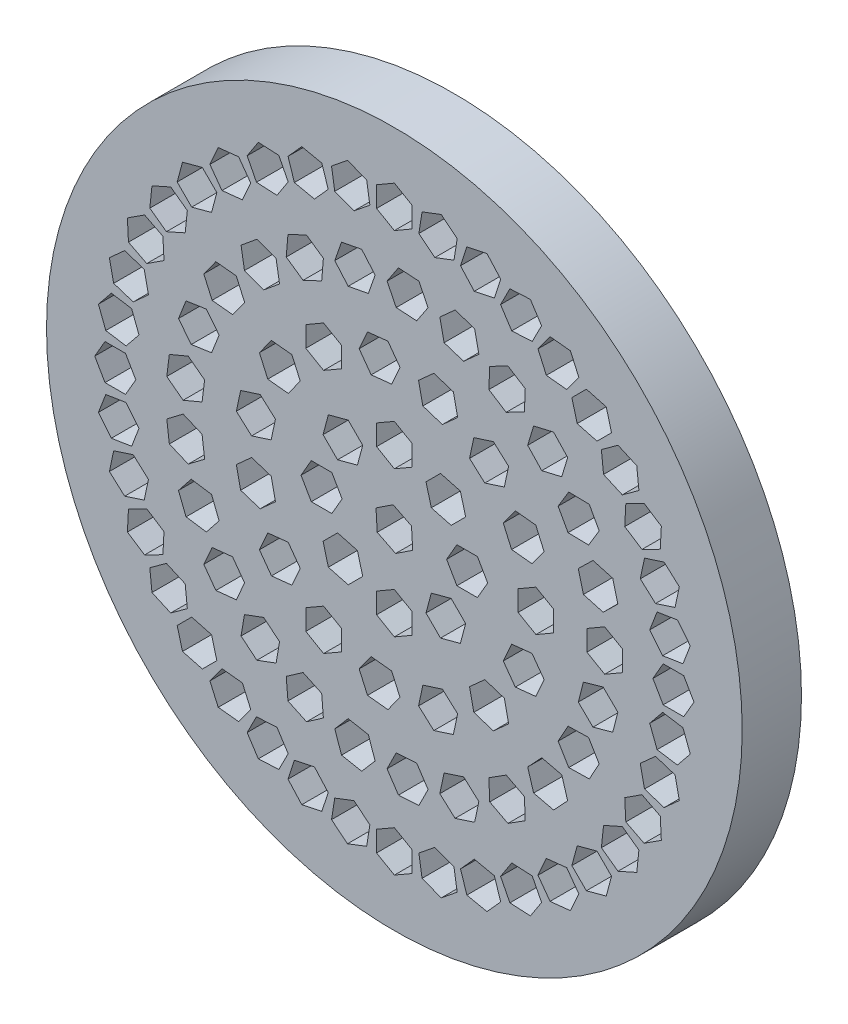
SolidWorks part; units mm, degrees
material "Balsa"
ref_plane "Front Plane" through (0, 0, 0) normal (0, 0, 1) x (1, 0, 0)
ref_plane "Top Plane" through (0, 0, 0) normal (0, 1, 0) x (1, 0, 0)
ref_plane "Right Plane" through (0, 0, 0) normal (1, 0, 0) x (0, 0, -1)
sketch "Sketch1" plane through (0, 0, 0) normal (0, 0, 1) x (1, 0, 0)
  line L0 (0, 44.3149) -> (0, -33.0251) construction
  line L1 (-45.3381, 0) -> (52.4482, 0) construction
  line L2 (29.34, 0) -> (23.54, 0) construction
  line L3 (23.54, 0) -> (17.74, 0) construction
  line L4 (17.74, 0) -> (11.94, 0) construction
  line L5 (11.94, 0) -> (6.14, 0) construction
  line L6 (3.1169, -3.1169) -> (2.6686, -4.7899)
  line L7 (7.8721, 0) -> (7.006, 1.5)
  line L8 (7.006, 1.5) -> (5.274, 1.5)
  line L9 (5.274, 1.5) -> (4.4079, 0)
  line L10 (4.4079, 0) -> (5.274, -1.5)
  line L11 (5.274, -1.5) -> (7.006, -1.5)
  line L12 (7.006, -1.5) -> (7.8721, 0)
  line L13 (11.94, -1.7321) -> (13.44, -0.866)
  line L14 (13.44, -0.866) -> (13.44, 0.866)
  line L15 (13.44, 0.866) -> (11.94, 1.7321)
  line L16 (11.94, 1.7321) -> (10.44, 0.866)
  line L17 (10.44, 0.866) -> (10.44, -0.866)
  line L18 (10.44, -0.866) -> (11.94, -1.7321)
  line L19 (17.74, -1.7321) -> (19.24, -0.866)
  line L20 (19.24, -0.866) -> (19.24, 0.866)
  line L21 (19.24, 0.866) -> (17.74, 1.7321)
  line L22 (17.74, 1.7321) -> (16.24, 0.866)
  line L23 (16.24, 0.866) -> (16.24, -0.866)
  line L24 (16.24, -0.866) -> (17.74, -1.7321)
  line L25 (21.8079, 0) -> (22.674, -1.5)
  line L26 (22.674, -1.5) -> (24.406, -1.5)
  line L27 (24.406, -1.5) -> (25.2721, 0)
  line L28 (25.2721, 0) -> (24.406, 1.5)
  line L29 (24.406, 1.5) -> (22.674, 1.5)
  line L30 (22.674, 1.5) -> (21.8079, 0)
  line L31 (4.7899, -2.6686) -> (3.1169, -3.1169)
  line L32 (6.0147, -3.8933) -> (4.7899, -2.6686)
  line L33 (5.5664, -5.5664) -> (6.0147, -3.8933)
  line L34 (3.8933, -6.0147) -> (5.5664, -5.5664)
  line L35 (2.6686, -4.7899) -> (3.8933, -6.0147)
  line L36 (0, -4.4079) -> (-1.5, -5.274)
  line L37 (1.5, -5.274) -> (0, -4.4079)
  line L38 (1.5, -7.006) -> (1.5, -5.274)
  line L39 (0, -7.8721) -> (1.5, -7.006)
  line L40 (-1.5, -7.006) -> (0, -7.8721)
  line L41 (-1.5, -5.274) -> (-1.5, -7.006)
  line L42 (-3.1169, -3.1169) -> (-4.7899, -2.6686)
  line L43 (-2.6686, -4.7899) -> (-3.1169, -3.1169)
  line L44 (-3.8933, -6.0147) -> (-2.6686, -4.7899)
  line L45 (-5.5664, -5.5664) -> (-3.8933, -6.0147)
  line L46 (-6.0147, -3.8933) -> (-5.5664, -5.5664)
  line L47 (-4.7899, -2.6686) -> (-6.0147, -3.8933)
  line L48 (-4.4079, 0) -> (-5.274, 1.5)
  line L49 (-5.274, -1.5) -> (-4.4079, 0)
  line L50 (-7.006, -1.5) -> (-5.274, -1.5)
  line L51 (-7.8721, 0) -> (-7.006, -1.5)
  line L52 (-7.006, 1.5) -> (-7.8721, 0)
  line L53 (-5.274, 1.5) -> (-7.006, 1.5)
  line L54 (-3.1169, 3.1169) -> (-2.6686, 4.7899)
  line L55 (-4.7899, 2.6686) -> (-3.1169, 3.1169)
  line L56 (-6.0147, 3.8933) -> (-4.7899, 2.6686)
  line L57 (-5.5664, 5.5664) -> (-6.0147, 3.8933)
  line L58 (-3.8933, 6.0147) -> (-5.5664, 5.5664)
  line L59 (-2.6686, 4.7899) -> (-3.8933, 6.0147)
  line L60 (0, 4.4079) -> (1.5, 5.274)
  line L61 (-1.5, 5.274) -> (0, 4.4079)
  line L62 (-1.5, 7.006) -> (-1.5, 5.274)
  line L63 (0, 7.8721) -> (-1.5, 7.006)
  line L64 (1.5, 7.006) -> (0, 7.8721)
  line L65 (1.5, 5.274) -> (1.5, 7.006)
  line L66 (3.1169, 3.1169) -> (4.7899, 2.6686)
  line L67 (2.6686, 4.7899) -> (3.1169, 3.1169)
  line L68 (3.8933, 6.0147) -> (2.6686, 4.7899)
  line L69 (5.5664, 5.5664) -> (3.8933, 6.0147)
  line L70 (6.0147, 3.8933) -> (5.5664, 5.5664)
  line L71 (4.7899, 2.6686) -> (6.0147, 3.8933)
  line L72 (9.1852, -5.0375) -> (10.2032, -6.4387)
  line L73 (1.5492, -0.7746) -> (1.4454, 0.9543)
  line L74 (1.4454, 0.9543) -> (-0.1038, 1.7289)
  line L75 (-0.1038, 1.7289) -> (-1.5492, 0.7746)
  line L76 (-1.5492, 0.7746) -> (-1.4454, -0.9543)
  line L77 (-1.4454, -0.9543) -> (0.1038, -1.7289)
  line L78 (0.1038, -1.7289) -> (1.5492, -0.7746)
  line L79 (10.2032, -6.4387) -> (11.9258, -6.2577)
  line L80 (11.9258, -6.2577) -> (12.6303, -4.6754)
  line L81 (12.6303, -4.6754) -> (11.6122, -3.2741)
  line L82 (11.6122, -3.2741) -> (9.8897, -3.4552)
  line L83 (9.8897, -3.4552) -> (9.1852, -5.0375)
  line L84 (6.3421, -8.3379) -> (6.7023, -10.0321)
  line L85 (6.7023, -10.0321) -> (8.3495, -10.5674)
  line L86 (8.3495, -10.5674) -> (9.6367, -9.4084)
  line L87 (9.6367, -9.4084) -> (9.2766, -7.7142)
  line L88 (9.2766, -7.7142) -> (7.6293, -7.1789)
  line L89 (7.6293, -7.1789) -> (6.3421, -8.3379)
  line L90 (2.4025, -10.1966) -> (2.0424, -11.8908)
  line L91 (2.0424, -11.8908) -> (3.3295, -13.0498)
  line L92 (3.3295, -13.0498) -> (4.9768, -12.5146)
  line L93 (4.9768, -12.5146) -> (5.3369, -10.8204)
  line L94 (5.3369, -10.8204) -> (4.0498, -9.6614)
  line L95 (4.0498, -9.6614) -> (2.4025, -10.1966)
  line L96 (-1.9526, -10.2923) -> (-2.9706, -11.6935)
  line L97 (-2.9706, -11.6935) -> (-2.2661, -13.2758)
  line L98 (-2.2661, -13.2758) -> (-0.5436, -13.4569)
  line L99 (-0.5436, -13.4569) -> (0.4745, -12.0556)
  line L100 (0.4745, -12.0556) -> (-0.23, -10.4733)
  line L101 (-0.23, -10.4733) -> (-1.9526, -10.2923)
  line L102 (-5.97, -8.6083) -> (-7.47, -9.4743)
  line L103 (-7.47, -9.4743) -> (-7.47, -11.2064)
  line L104 (-7.47, -11.2064) -> (-5.97, -12.0724)
  line L105 (-5.97, -12.0724) -> (-4.47, -11.2064)
  line L106 (-4.47, -11.2064) -> (-4.47, -9.4743)
  line L107 (-4.47, -9.4743) -> (-5.97, -8.6083)
  line L108 (-8.9552, -5.4358) -> (-10.6777, -5.6169)
  line L109 (-10.6777, -5.6169) -> (-11.3822, -7.1992)
  line L110 (-11.3822, -7.1992) -> (-10.3642, -8.6005)
  line L111 (-10.3642, -8.6005) -> (-8.6416, -8.4194)
  line L112 (-8.6416, -8.4194) -> (-7.9371, -6.8371)
  line L113 (-7.9371, -6.8371) -> (-8.9552, -5.4358)
  line L114 (-10.3919, -1.3235) -> (-12.0392, -0.7883)
  line L115 (-12.0392, -0.7883) -> (-13.3264, -1.9472)
  line L116 (-13.3264, -1.9472) -> (-12.9662, -3.6414)
  line L117 (-12.9662, -3.6414) -> (-11.319, -4.1767)
  line L118 (-11.319, -4.1767) -> (-10.0318, -3.0177)
  line L119 (-10.0318, -3.0177) -> (-10.3919, -1.3235)
  line L120 (-10.0318, 3.0177) -> (-11.319, 4.1767)
  line L121 (-11.319, 4.1767) -> (-12.9662, 3.6414)
  line L122 (-12.9662, 3.6414) -> (-13.3264, 1.9472)
  line L123 (-13.3264, 1.9472) -> (-12.0392, 0.7883)
  line L124 (-12.0392, 0.7883) -> (-10.3919, 1.3235)
  line L125 (-10.3919, 1.3235) -> (-10.0318, 3.0177)
  line L126 (-7.9371, 6.8371) -> (-8.6416, 8.4194)
  line L127 (-8.6416, 8.4194) -> (-10.3642, 8.6005)
  line L128 (-10.3642, 8.6005) -> (-11.3822, 7.1992)
  line L129 (-11.3822, 7.1992) -> (-10.6777, 5.6169)
  line L130 (-10.6777, 5.6169) -> (-8.9552, 5.4358)
  line L131 (-8.9552, 5.4358) -> (-7.9371, 6.8371)
  line L132 (-4.47, 9.4743) -> (-4.47, 11.2064)
  line L133 (-4.47, 11.2064) -> (-5.97, 12.0724)
  line L134 (-5.97, 12.0724) -> (-7.47, 11.2064)
  line L135 (-7.47, 11.2064) -> (-7.47, 9.4743)
  line L136 (-7.47, 9.4743) -> (-5.97, 8.6083)
  line L137 (-5.97, 8.6083) -> (-4.47, 9.4743)
  line L138 (-0.23, 10.4733) -> (0.4745, 12.0556)
  line L139 (0.4745, 12.0556) -> (-0.5436, 13.4569)
  line L140 (-0.5436, 13.4569) -> (-2.2661, 13.2758)
  line L141 (-2.2661, 13.2758) -> (-2.9706, 11.6935)
  line L142 (-2.9706, 11.6935) -> (-1.9526, 10.2923)
  line L143 (-1.9526, 10.2923) -> (-0.23, 10.4733)
  line L144 (4.0498, 9.6614) -> (5.3369, 10.8204)
  line L145 (5.3369, 10.8204) -> (4.9768, 12.5146)
  line L146 (4.9768, 12.5146) -> (3.3295, 13.0498)
  line L147 (3.3295, 13.0498) -> (2.0424, 11.8908)
  line L148 (2.0424, 11.8908) -> (2.4025, 10.1966)
  line L149 (2.4025, 10.1966) -> (4.0498, 9.6614)
  line L150 (7.6293, 7.1789) -> (9.2766, 7.7142)
  line L151 (9.2766, 7.7142) -> (9.6367, 9.4084)
  line L152 (9.6367, 9.4084) -> (8.3495, 10.5674)
  line L153 (8.3495, 10.5674) -> (6.7023, 10.0321)
  line L154 (6.7023, 10.0321) -> (6.3421, 8.3379)
  line L155 (6.3421, 8.3379) -> (7.6293, 7.1789)
  line L156 (9.8897, 3.4552) -> (11.6122, 3.2741)
  line L157 (11.6122, 3.2741) -> (12.6303, 4.6754)
  line L158 (12.6303, 4.6754) -> (11.9258, 6.2577)
  line L159 (11.9258, 6.2577) -> (10.2032, 6.4387)
  line L160 (10.2032, 6.4387) -> (9.1852, 5.0375)
  line L161 (9.1852, 5.0375) -> (9.8897, 3.4552)
  line L162 (16.7519, -6.0894) -> (18.4202, -5.6236)
  line L163 (15.5144, -4.8775) -> (16.7519, -6.0894)
  line L164 (15.9452, -3.1999) -> (15.5144, -4.8775)
  line L165 (17.6134, -2.7341) -> (15.9452, -3.1999)
  line L166 (18.8509, -3.946) -> (17.6134, -2.7341)
  line L167 (18.4202, -5.6236) -> (18.8509, -3.946)
  line L168 (14.7113, -10.0641) -> (16.4429, -10.0278)
  line L169 (13.814, -8.5826) -> (14.7113, -10.0641)
  line L170 (14.6484, -7.0648) -> (13.814, -8.5826)
  line L171 (16.3801, -7.0285) -> (14.6484, -7.0648)
  line L172 (17.2774, -8.51) -> (16.3801, -7.0285)
  line L173 (16.4429, -10.0278) -> (17.2774, -8.51)
  line L174 (11.7462, -13.4065) -> (13.4325, -13.802)
  line L175 (11.2456, -11.7484) -> (11.7462, -13.4065)
  line L176 (12.4313, -10.4857) -> (11.2456, -11.7484)
  line L177 (14.1176, -10.8813) -> (12.4313, -10.4857)
  line L178 (14.6182, -12.5394) -> (14.1176, -10.8813)
  line L179 (13.4325, -13.802) -> (14.6182, -12.5394)
  line L180 (8.0431, -15.9065) -> (9.5781, -16.7089)
  line L181 (7.9706, -14.1759) -> (8.0431, -15.9065)
  line L182 (9.433, -13.2478) -> (7.9706, -14.1759)
  line L183 (10.968, -14.0503) -> (9.433, -13.2478)
  line L184 (11.0405, -15.7808) -> (10.968, -14.0503)
  line L185 (9.5781, -16.7089) -> (11.0405, -15.7808)
  line L186 (3.8347, -17.407) -> (5.1218, -18.5659)
  line L187 (4.1948, -15.7128) -> (3.8347, -17.407)
  line L188 (5.8421, -15.1775) -> (4.1948, -15.7128)
  line L189 (7.1292, -16.3365) -> (5.8421, -15.1775)
  line L190 (6.7691, -18.0307) -> (7.1292, -16.3365)
  line L191 (5.1218, -18.5659) -> (6.7691, -18.0307)
  line L192 (-0.6147, -17.8138) -> (0.3438, -19.2564)
  line L193 (0.1554, -16.2623) -> (-0.6147, -17.8138)
  line L194 (1.884, -16.1536) -> (0.1554, -16.2623)
  line L195 (2.8425, -17.5962) -> (1.884, -16.1536)
  line L196 (2.0724, -19.1477) -> (2.8425, -17.5962)
  line L197 (0.3438, -19.2564) -> (2.0724, -19.1477)
  line L198 (-5.0255, -17.1012) -> (-4.4559, -18.7369)
  line L199 (-3.8938, -15.7901) -> (-5.0255, -17.1012)
  line L200 (-2.1924, -16.1146) -> (-3.8938, -15.7901)
  line L201 (-1.6228, -17.7503) -> (-2.1924, -16.1146)
  line L202 (-2.7545, -19.0615) -> (-1.6228, -17.7503)
  line L203 (-4.4559, -18.7369) -> (-2.7545, -19.0615)
  line L204 (-9.1205, -15.3142) -> (-8.9756, -17.0401)
  line L205 (-7.6983, -14.3257) -> (-9.1205, -15.3142)
  line L206 (-6.1311, -15.0631) -> (-7.6983, -14.3257)
  line L207 (-5.9861, -16.7891) -> (-6.1311, -15.0631)
  line L208 (-7.4084, -17.7776) -> (-5.9861, -16.7891)
  line L209 (-8.9756, -17.0401) -> (-7.4084, -17.7776)
  line L210 (-12.6425, -12.5649) -> (-12.9313, -14.2726)
  line L211 (-11.019, -11.9611) -> (-12.6425, -12.5649)
  line L212 (-9.6845, -13.0652) -> (-11.019, -11.9611)
  line L213 (-9.9733, -14.773) -> (-9.6845, -13.0652)
  line L214 (-11.5968, -15.3767) -> (-9.9733, -14.773)
  line L215 (-12.9313, -14.2726) -> (-11.5968, -15.3767)
  line L216 (-15.37, -9.0261) -> (-16.0745, -10.6084)
  line L217 (-13.6475, -8.845) -> (-15.37, -9.0261)
  line L218 (-12.6294, -10.2463) -> (-13.6475, -8.845)
  line L219 (-13.3339, -11.8286) -> (-12.6294, -10.2463)
  line L220 (-15.0565, -12.0096) -> (-13.3339, -11.8286)
  line L221 (-16.0745, -10.6084) -> (-15.0565, -12.0096)
  line L222 (-17.1318, -4.9201) -> (-18.2077, -6.2775)
  line L223 (-15.4184, -5.1731) -> (-17.1318, -4.9201)
  line L224 (-14.7808, -6.7836) -> (-15.4184, -5.1731)
  line L225 (-15.8566, -8.1409) -> (-14.7808, -6.7836)
  line L226 (-17.5701, -7.8879) -> (-15.8566, -8.1409)
  line L227 (-18.2077, -6.2775) -> (-17.5701, -7.8879)
  line L228 (-17.8172, -0.505) -> (-19.1968, -1.5522)
  line L229 (-16.2205, -1.1762) -> (-17.8172, -0.505)
  line L230 (-16.0034, -2.8946) -> (-16.2205, -1.1762)
  line L231 (-17.383, -3.9418) -> (-16.0034, -2.8946)
  line L232 (-18.9797, -3.2706) -> (-17.383, -3.9418)
  line L233 (-19.1968, -1.5522) -> (-18.9797, -3.2706)
  line L234 (-17.383, 3.9418) -> (-18.9797, 3.2706)
  line L235 (-16.0034, 2.8946) -> (-17.383, 3.9418)
  line L236 (-16.2205, 1.1762) -> (-16.0034, 2.8946)
  line L237 (-17.8172, 0.505) -> (-16.2205, 1.1762)
  line L238 (-19.1968, 1.5522) -> (-17.8172, 0.505)
  line L239 (-18.9797, 3.2706) -> (-19.1968, 1.5522)
  line L240 (-15.8566, 8.1409) -> (-17.5701, 7.8879)
  line L241 (-14.7808, 6.7836) -> (-15.8566, 8.1409)
  line L242 (-15.4184, 5.1731) -> (-14.7808, 6.7836)
  line L243 (-17.1318, 4.9201) -> (-15.4184, 5.1731)
  line L244 (-18.2077, 6.2775) -> (-17.1318, 4.9201)
  line L245 (-17.5701, 7.8879) -> (-18.2077, 6.2775)
  line L246 (-13.3339, 11.8286) -> (-15.0565, 12.0096)
  line L247 (-12.6294, 10.2463) -> (-13.3339, 11.8286)
  line L248 (-13.6475, 8.845) -> (-12.6294, 10.2463)
  line L249 (-15.37, 9.0261) -> (-13.6475, 8.845)
  line L250 (-16.0745, 10.6084) -> (-15.37, 9.0261)
  line L251 (-15.0565, 12.0096) -> (-16.0745, 10.6084)
  line L252 (-9.9733, 14.773) -> (-11.5968, 15.3767)
  line L253 (-9.6845, 13.0652) -> (-9.9733, 14.773)
  line L254 (-11.019, 11.9611) -> (-9.6845, 13.0652)
  line L255 (-12.6425, 12.5649) -> (-11.019, 11.9611)
  line L256 (-12.9313, 14.2726) -> (-12.6425, 12.5649)
  line L257 (-11.5968, 15.3767) -> (-12.9313, 14.2726)
  line L258 (-5.9861, 16.7891) -> (-7.4084, 17.7776)
  line L259 (-6.1311, 15.0631) -> (-5.9861, 16.7891)
  line L260 (-7.6983, 14.3257) -> (-6.1311, 15.0631)
  line L261 (-9.1205, 15.3142) -> (-7.6983, 14.3257)
  line L262 (-8.9756, 17.0401) -> (-9.1205, 15.3142)
  line L263 (-7.4084, 17.7776) -> (-8.9756, 17.0401)
  line L264 (-1.6228, 17.7503) -> (-2.7545, 19.0615)
  line L265 (-2.1924, 16.1146) -> (-1.6228, 17.7503)
  line L266 (-3.8938, 15.7901) -> (-2.1924, 16.1146)
  line L267 (-5.0255, 17.1012) -> (-3.8938, 15.7901)
  line L268 (-4.4559, 18.7369) -> (-5.0255, 17.1012)
  line L269 (-2.7545, 19.0615) -> (-4.4559, 18.7369)
  line L270 (2.8425, 17.5962) -> (2.0724, 19.1477)
  line L271 (1.884, 16.1536) -> (2.8425, 17.5962)
  line L272 (0.1554, 16.2623) -> (1.884, 16.1536)
  line L273 (-0.6147, 17.8138) -> (0.1554, 16.2623)
  line L274 (0.3438, 19.2564) -> (-0.6147, 17.8138)
  line L275 (2.0724, 19.1477) -> (0.3438, 19.2564)
  line L276 (7.1292, 16.3365) -> (6.7691, 18.0307)
  line L277 (5.8421, 15.1775) -> (7.1292, 16.3365)
  line L278 (4.1948, 15.7128) -> (5.8421, 15.1775)
  line L279 (3.8347, 17.407) -> (4.1948, 15.7128)
  line L280 (5.1218, 18.5659) -> (3.8347, 17.407)
  line L281 (6.7691, 18.0307) -> (5.1218, 18.5659)
  line L282 (10.968, 14.0503) -> (11.0405, 15.7808)
  line L283 (9.433, 13.2478) -> (10.968, 14.0503)
  line L284 (7.9706, 14.1759) -> (9.433, 13.2478)
  line L285 (8.0431, 15.9065) -> (7.9706, 14.1759)
  line L286 (9.5781, 16.7089) -> (8.0431, 15.9065)
  line L287 (11.0405, 15.7808) -> (9.5781, 16.7089)
  line L288 (14.1176, 10.8813) -> (14.6182, 12.5394)
  line L289 (12.4313, 10.4857) -> (14.1176, 10.8813)
  line L290 (11.2456, 11.7484) -> (12.4313, 10.4857)
  line L291 (11.7462, 13.4065) -> (11.2456, 11.7484)
  line L292 (13.4325, 13.802) -> (11.7462, 13.4065)
  line L293 (14.6182, 12.5394) -> (13.4325, 13.802)
  line L294 (16.3801, 7.0285) -> (17.2774, 8.51)
  line L295 (14.6484, 7.0648) -> (16.3801, 7.0285)
  line L296 (13.814, 8.5826) -> (14.6484, 7.0648)
  line L297 (14.7113, 10.0641) -> (13.814, 8.5826)
  line L298 (16.4429, 10.0278) -> (14.7113, 10.0641)
  line L299 (17.2774, 8.51) -> (16.4429, 10.0278)
  line L300 (17.6134, 2.7341) -> (18.8509, 3.946)
  line L301 (15.9452, 3.1999) -> (17.6134, 2.7341)
  line L302 (15.5144, 4.8775) -> (15.9452, 3.1999)
  line L303 (16.7519, 6.0894) -> (15.5144, 4.8775)
  line L304 (18.4202, 5.6236) -> (16.7519, 6.0894)
  line L305 (18.8509, 3.946) -> (18.4202, 5.6236)
  line L306 (21.5395, -3.4115) -> (22.1602, -5.0285)
  line L307 (22.6295, -2.0655) -> (21.5395, -3.4115)
  line L308 (24.3402, -2.3364) -> (22.6295, -2.0655)
  line L309 (24.9609, -3.9534) -> (24.3402, -2.3364)
  line L310 (23.8709, -5.2995) -> (24.9609, -3.9534)
  line L311 (22.1602, -5.0285) -> (23.8709, -5.2995)
  line L312 (20.7406, -6.739) -> (21.1007, -8.4332)
  line L313 (22.0278, -5.5801) -> (20.7406, -6.739)
  line L314 (23.675, -6.1153) -> (22.0278, -5.5801)
  line L315 (24.0351, -7.8095) -> (23.675, -6.1153)
  line L316 (22.748, -8.9685) -> (24.0351, -7.8095)
  line L317 (21.1007, -8.4332) -> (22.748, -8.9685)
  line L318 (19.431, -9.9006) -> (19.5217, -11.6303)
  line L319 (20.8836, -8.9573) -> (19.431, -9.9006)
  line L320 (22.4269, -9.7436) -> (20.8836, -8.9573)
  line L321 (22.5176, -11.4733) -> (22.4269, -9.7436)
  line L322 (21.0649, -12.4166) -> (22.5176, -11.4733)
  line L323 (19.5217, -11.6303) -> (21.0649, -12.4166)
  line L324 (17.643, -12.8184) -> (17.462, -14.541)
  line L325 (19.2253, -12.1139) -> (17.643, -12.8184)
  line L326 (20.6266, -13.132) -> (19.2253, -12.1139)
  line L327 (20.4455, -14.8545) -> (20.6266, -13.132)
  line L328 (18.8632, -15.559) -> (20.4455, -14.8545)
  line L329 (17.462, -14.541) -> (18.8632, -15.559)
  line L330 (15.4205, -15.4205) -> (14.9723, -17.0936)
  line L331 (17.0936, -14.9723) -> (15.4205, -15.4205)
  line L332 (18.3183, -16.197) -> (17.0936, -14.9723)
  line L333 (17.87, -17.87) -> (18.3183, -16.197)
  line L334 (16.197, -18.3183) -> (17.87, -17.87)
  line L335 (14.9723, -17.0936) -> (16.197, -18.3183)
  line L336 (12.8184, -17.643) -> (12.1139, -19.2253)
  line L337 (14.541, -17.462) -> (12.8184, -17.643)
  line L338 (15.559, -18.8632) -> (14.541, -17.462)
  line L339 (14.8545, -20.4455) -> (15.559, -18.8632)
  line L340 (13.132, -20.6266) -> (14.8545, -20.4455)
  line L341 (12.1139, -19.2253) -> (13.132, -20.6266)
  line L342 (9.9006, -19.431) -> (8.9573, -20.8836)
  line L343 (11.6303, -19.5217) -> (9.9006, -19.431)
  line L344 (12.4166, -21.0649) -> (11.6303, -19.5217)
  line L345 (11.4733, -22.5176) -> (12.4166, -21.0649)
  line L346 (9.7436, -22.4269) -> (11.4733, -22.5176)
  line L347 (8.9573, -20.8836) -> (9.7436, -22.4269)
  line L348 (6.739, -20.7406) -> (5.5801, -22.0278)
  line L349 (8.4332, -21.1007) -> (6.739, -20.7406)
  line L350 (8.9685, -22.748) -> (8.4332, -21.1007)
  line L351 (7.8095, -24.0351) -> (8.9685, -22.748)
  line L352 (6.1153, -23.675) -> (7.8095, -24.0351)
  line L353 (5.5801, -22.0278) -> (6.1153, -23.675)
  line L354 (3.4115, -21.5395) -> (2.0655, -22.6295)
  line L355 (5.0285, -22.1602) -> (3.4115, -21.5395)
  line L356 (5.2995, -23.8709) -> (5.0285, -22.1602)
  line L357 (3.9534, -24.9609) -> (5.2995, -23.8709)
  line L358 (2.3364, -24.3402) -> (3.9534, -24.9609)
  line L359 (2.0655, -22.6295) -> (2.3364, -24.3402)
  line L360 (0, -21.8079) -> (-1.5, -22.674)
  line L361 (1.5, -22.674) -> (0, -21.8079)
  line L362 (1.5, -24.406) -> (1.5, -22.674)
  line L363 (0, -25.2721) -> (1.5, -24.406)
  line L364 (-1.5, -24.406) -> (0, -25.2721)
  line L365 (-1.5, -22.674) -> (-1.5, -24.406)
  line L366 (-3.4115, -21.5395) -> (-5.0285, -22.1602)
  line L367 (-2.0655, -22.6295) -> (-3.4115, -21.5395)
  line L368 (-2.3364, -24.3402) -> (-2.0655, -22.6295)
  line L369 (-3.9534, -24.9609) -> (-2.3364, -24.3402)
  line L370 (-5.2995, -23.8709) -> (-3.9534, -24.9609)
  line L371 (-5.0285, -22.1602) -> (-5.2995, -23.8709)
  line L372 (-6.739, -20.7406) -> (-8.4332, -21.1007)
  line L373 (-5.5801, -22.0278) -> (-6.739, -20.7406)
  line L374 (-6.1153, -23.675) -> (-5.5801, -22.0278)
  line L375 (-7.8095, -24.0351) -> (-6.1153, -23.675)
  line L376 (-8.9685, -22.748) -> (-7.8095, -24.0351)
  line L377 (-8.4332, -21.1007) -> (-8.9685, -22.748)
  line L378 (-9.9006, -19.431) -> (-11.6303, -19.5217)
  line L379 (-8.9573, -20.8836) -> (-9.9006, -19.431)
  line L380 (-9.7436, -22.4269) -> (-8.9573, -20.8836)
  line L381 (-11.4733, -22.5176) -> (-9.7436, -22.4269)
  line L382 (-12.4166, -21.0649) -> (-11.4733, -22.5176)
  line L383 (-11.6303, -19.5217) -> (-12.4166, -21.0649)
  line L384 (-12.8184, -17.643) -> (-14.541, -17.462)
  line L385 (-12.1139, -19.2253) -> (-12.8184, -17.643)
  line L386 (-13.132, -20.6266) -> (-12.1139, -19.2253)
  line L387 (-14.8545, -20.4455) -> (-13.132, -20.6266)
  line L388 (-15.559, -18.8632) -> (-14.8545, -20.4455)
  line L389 (-14.541, -17.462) -> (-15.559, -18.8632)
  line L390 (-15.4205, -15.4205) -> (-17.0936, -14.9723)
  line L391 (-14.9723, -17.0936) -> (-15.4205, -15.4205)
  line L392 (-16.197, -18.3183) -> (-14.9723, -17.0936)
  line L393 (-17.87, -17.87) -> (-16.197, -18.3183)
  line L394 (-18.3183, -16.197) -> (-17.87, -17.87)
  line L395 (-17.0936, -14.9723) -> (-18.3183, -16.197)
  line L396 (-17.643, -12.8184) -> (-19.2253, -12.1139)
  line L397 (-17.462, -14.541) -> (-17.643, -12.8184)
  line L398 (-18.8632, -15.559) -> (-17.462, -14.541)
  line L399 (-20.4455, -14.8545) -> (-18.8632, -15.559)
  line L400 (-20.6266, -13.132) -> (-20.4455, -14.8545)
  line L401 (-19.2253, -12.1139) -> (-20.6266, -13.132)
  line L402 (-19.431, -9.9006) -> (-20.8836, -8.9573)
  line L403 (-19.5217, -11.6303) -> (-19.431, -9.9006)
  line L404 (-21.0649, -12.4166) -> (-19.5217, -11.6303)
  line L405 (-22.5176, -11.4733) -> (-21.0649, -12.4166)
  line L406 (-22.4269, -9.7436) -> (-22.5176, -11.4733)
  line L407 (-20.8836, -8.9573) -> (-22.4269, -9.7436)
  line L408 (-20.7406, -6.739) -> (-22.0278, -5.5801)
  line L409 (-21.1007, -8.4332) -> (-20.7406, -6.739)
  line L410 (-22.748, -8.9685) -> (-21.1007, -8.4332)
  line L411 (-24.0351, -7.8095) -> (-22.748, -8.9685)
  line L412 (-23.675, -6.1153) -> (-24.0351, -7.8095)
  line L413 (-22.0278, -5.5801) -> (-23.675, -6.1153)
  line L414 (-21.5395, -3.4115) -> (-22.6295, -2.0655)
  line L415 (-22.1602, -5.0285) -> (-21.5395, -3.4115)
  line L416 (-23.8709, -5.2995) -> (-22.1602, -5.0285)
  line L417 (-24.9609, -3.9534) -> (-23.8709, -5.2995)
  line L418 (-24.3402, -2.3364) -> (-24.9609, -3.9534)
  line L419 (-22.6295, -2.0655) -> (-24.3402, -2.3364)
  line L420 (-21.8079, 0) -> (-22.674, 1.5)
  line L421 (-22.674, -1.5) -> (-21.8079, 0)
  line L422 (-24.406, -1.5) -> (-22.674, -1.5)
  line L423 (-25.2721, 0) -> (-24.406, -1.5)
  line L424 (-24.406, 1.5) -> (-25.2721, 0)
  line L425 (-22.674, 1.5) -> (-24.406, 1.5)
  line L426 (-21.5395, 3.4115) -> (-22.1602, 5.0285)
  line L427 (-22.6295, 2.0655) -> (-21.5395, 3.4115)
  line L428 (-24.3402, 2.3364) -> (-22.6295, 2.0655)
  line L429 (-24.9609, 3.9534) -> (-24.3402, 2.3364)
  line L430 (-23.8709, 5.2995) -> (-24.9609, 3.9534)
  line L431 (-22.1602, 5.0285) -> (-23.8709, 5.2995)
  line L432 (-20.7406, 6.739) -> (-21.1007, 8.4332)
  line L433 (-22.0278, 5.5801) -> (-20.7406, 6.739)
  line L434 (-23.675, 6.1153) -> (-22.0278, 5.5801)
  line L435 (-24.0351, 7.8095) -> (-23.675, 6.1153)
  line L436 (-22.748, 8.9685) -> (-24.0351, 7.8095)
  line L437 (-21.1007, 8.4332) -> (-22.748, 8.9685)
  line L438 (-19.431, 9.9006) -> (-19.5217, 11.6303)
  line L439 (-20.8836, 8.9573) -> (-19.431, 9.9006)
  line L440 (-22.4269, 9.7436) -> (-20.8836, 8.9573)
  line L441 (-22.5176, 11.4733) -> (-22.4269, 9.7436)
  line L442 (-21.0649, 12.4166) -> (-22.5176, 11.4733)
  line L443 (-19.5217, 11.6303) -> (-21.0649, 12.4166)
  line L444 (-17.643, 12.8184) -> (-17.462, 14.541)
  line L445 (-19.2253, 12.1139) -> (-17.643, 12.8184)
  line L446 (-20.6266, 13.132) -> (-19.2253, 12.1139)
  line L447 (-20.4455, 14.8545) -> (-20.6266, 13.132)
  line L448 (-18.8632, 15.559) -> (-20.4455, 14.8545)
  line L449 (-17.462, 14.541) -> (-18.8632, 15.559)
  line L450 (-15.4205, 15.4205) -> (-14.9723, 17.0936)
  line L451 (-17.0936, 14.9723) -> (-15.4205, 15.4205)
  line L452 (-18.3183, 16.197) -> (-17.0936, 14.9723)
  line L453 (-17.87, 17.87) -> (-18.3183, 16.197)
  line L454 (-16.197, 18.3183) -> (-17.87, 17.87)
  line L455 (-14.9723, 17.0936) -> (-16.197, 18.3183)
  line L456 (-12.8184, 17.643) -> (-12.1139, 19.2253)
  line L457 (-14.541, 17.462) -> (-12.8184, 17.643)
  line L458 (-15.559, 18.8632) -> (-14.541, 17.462)
  line L459 (-14.8545, 20.4455) -> (-15.559, 18.8632)
  line L460 (-13.132, 20.6266) -> (-14.8545, 20.4455)
  line L461 (-12.1139, 19.2253) -> (-13.132, 20.6266)
  line L462 (-9.9006, 19.431) -> (-8.9573, 20.8836)
  line L463 (-11.6303, 19.5217) -> (-9.9006, 19.431)
  line L464 (-12.4166, 21.0649) -> (-11.6303, 19.5217)
  line L465 (-11.4733, 22.5176) -> (-12.4166, 21.0649)
  line L466 (-9.7436, 22.4269) -> (-11.4733, 22.5176)
  line L467 (-8.9573, 20.8836) -> (-9.7436, 22.4269)
  line L468 (-6.739, 20.7406) -> (-5.5801, 22.0278)
  line L469 (-8.4332, 21.1007) -> (-6.739, 20.7406)
  line L470 (-8.9685, 22.748) -> (-8.4332, 21.1007)
  line L471 (-7.8095, 24.0351) -> (-8.9685, 22.748)
  line L472 (-6.1153, 23.675) -> (-7.8095, 24.0351)
  line L473 (-5.5801, 22.0278) -> (-6.1153, 23.675)
  line L474 (-3.4115, 21.5395) -> (-2.0655, 22.6295)
  line L475 (-5.0285, 22.1602) -> (-3.4115, 21.5395)
  line L476 (-5.2995, 23.8709) -> (-5.0285, 22.1602)
  line L477 (-3.9534, 24.9609) -> (-5.2995, 23.8709)
  line L478 (-2.3364, 24.3402) -> (-3.9534, 24.9609)
  line L479 (-2.0655, 22.6295) -> (-2.3364, 24.3402)
  line L480 (0, 21.8079) -> (1.5, 22.674)
  line L481 (-1.5, 22.674) -> (0, 21.8079)
  line L482 (-1.5, 24.406) -> (-1.5, 22.674)
  line L483 (0, 25.2721) -> (-1.5, 24.406)
  line L484 (1.5, 24.406) -> (0, 25.2721)
  line L485 (1.5, 22.674) -> (1.5, 24.406)
  line L486 (3.4115, 21.5395) -> (5.0285, 22.1602)
  line L487 (2.0655, 22.6295) -> (3.4115, 21.5395)
  line L488 (2.3364, 24.3402) -> (2.0655, 22.6295)
  line L489 (3.9534, 24.9609) -> (2.3364, 24.3402)
  line L490 (5.2995, 23.8709) -> (3.9534, 24.9609)
  line L491 (5.0285, 22.1602) -> (5.2995, 23.8709)
  line L492 (6.739, 20.7406) -> (8.4332, 21.1007)
  line L493 (5.5801, 22.0278) -> (6.739, 20.7406)
  line L494 (6.1153, 23.675) -> (5.5801, 22.0278)
  line L495 (7.8095, 24.0351) -> (6.1153, 23.675)
  line L496 (8.9685, 22.748) -> (7.8095, 24.0351)
  line L497 (8.4332, 21.1007) -> (8.9685, 22.748)
  line L498 (9.9006, 19.431) -> (11.6303, 19.5217)
  line L499 (8.9573, 20.8836) -> (9.9006, 19.431)
  line L500 (9.7436, 22.4269) -> (8.9573, 20.8836)
  line L501 (11.4733, 22.5176) -> (9.7436, 22.4269)
  line L502 (12.4166, 21.0649) -> (11.4733, 22.5176)
  line L503 (11.6303, 19.5217) -> (12.4166, 21.0649)
  line L504 (12.8184, 17.643) -> (14.541, 17.462)
  line L505 (12.1139, 19.2253) -> (12.8184, 17.643)
  line L506 (13.132, 20.6266) -> (12.1139, 19.2253)
  line L507 (14.8545, 20.4455) -> (13.132, 20.6266)
  line L508 (15.559, 18.8632) -> (14.8545, 20.4455)
  line L509 (14.541, 17.462) -> (15.559, 18.8632)
  line L510 (15.4205, 15.4205) -> (17.0936, 14.9723)
  line L511 (14.9723, 17.0936) -> (15.4205, 15.4205)
  line L512 (16.197, 18.3183) -> (14.9723, 17.0936)
  line L513 (17.87, 17.87) -> (16.197, 18.3183)
  line L514 (18.3183, 16.197) -> (17.87, 17.87)
  line L515 (17.0936, 14.9723) -> (18.3183, 16.197)
  line L516 (17.643, 12.8184) -> (19.2253, 12.1139)
  line L517 (17.462, 14.541) -> (17.643, 12.8184)
  line L518 (18.8632, 15.559) -> (17.462, 14.541)
  line L519 (20.4455, 14.8545) -> (18.8632, 15.559)
  line L520 (20.6266, 13.132) -> (20.4455, 14.8545)
  line L521 (19.2253, 12.1139) -> (20.6266, 13.132)
  line L522 (19.431, 9.9006) -> (20.8836, 8.9573)
  line L523 (19.5217, 11.6303) -> (19.431, 9.9006)
  line L524 (21.0649, 12.4166) -> (19.5217, 11.6303)
  line L525 (22.5176, 11.4733) -> (21.0649, 12.4166)
  line L526 (22.4269, 9.7436) -> (22.5176, 11.4733)
  line L527 (20.8836, 8.9573) -> (22.4269, 9.7436)
  line L528 (20.7406, 6.739) -> (22.0278, 5.5801)
  line L529 (21.1007, 8.4332) -> (20.7406, 6.739)
  line L530 (22.748, 8.9685) -> (21.1007, 8.4332)
  line L531 (24.0351, 7.8095) -> (22.748, 8.9685)
  line L532 (23.675, 6.1153) -> (24.0351, 7.8095)
  line L533 (22.0278, 5.5801) -> (23.675, 6.1153)
  line L534 (21.5395, 3.4115) -> (22.6295, 2.0655)
  line L535 (22.1602, 5.0285) -> (21.5395, 3.4115)
  line L536 (23.8709, 5.2995) -> (22.1602, 5.0285)
  line L537 (24.9609, 3.9534) -> (23.8709, 5.2995)
  line L538 (24.3402, 2.3364) -> (24.9609, 3.9534)
  line L539 (22.6295, 2.0655) -> (24.3402, 2.3364)
  circle A0 centre (0, 0) radius 29.34
  circle A1 centre (6.14, 0) radius 1.5 construction
  circle A2 centre (11.94, 0) radius 1.5 construction
  circle A3 centre (17.74, 0) radius 1.5 construction
  circle A4 centre (23.54, 0) radius 1.5 construction
  circle A5 centre (0, 0) radius 1.5 construction
  point P85 (0, 0)
  point P177 (0, 0)
  point P322 (0, 0)
  point P557 (0, 0)
  dimension "D1" = 8
  dimension "D2" = 15
  dimension "D3" = 25
  dimension "D4" = 40
extrude "Boss-Extrude1" add sketch "Sketch1" along normal blind 5
